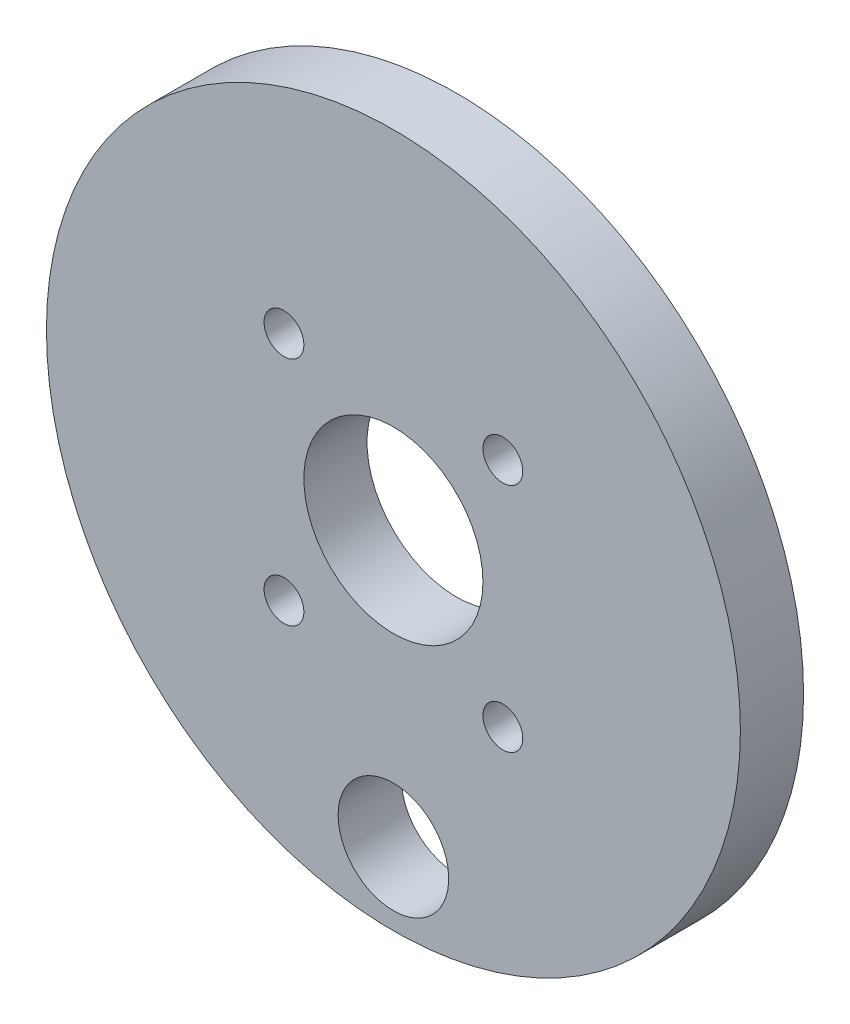
SolidWorks part; units mm, degrees
material "Plain Carbon Steel"
ref_plane "Front Plane" through (0, 0, 0) normal (0, 0, 1) x (1, 0, 0)
ref_plane "Top Plane" through (0, 0, 0) normal (0, 1, 0) x (1, 0, 0)
ref_plane "Right Plane" through (0, 0, 0) normal (1, 0, 0) x (0, 0, -1)
sketch "Sketch1" plane through (0, 0, 0) normal (0, 0, 1) x (1, 0, 0)
  circle A0 centre (0, 0) radius 34.875
  circle A1 centre (0, 0) radius 9
  dimension "D1" = 69.75
  dimension "D2" = 18
extrude "Boss-Extrude1" add sketch "Sketch1" along normal blind 6.35
sketch "Sketch2" plane through (0, 0, 0) normal (0, 0, -1) x (-1, 0, 0)
  circle A0 centre (-11, 11.619) radius 2
  circle A1 centre (11, 11.619) radius 2
  circle A2 centre (11, -11.619) radius 2
  circle A3 centre (-11, -11.619) radius 2
  point P0 (-11, 11.619)
  point P1 (11, 11.619)
  point P3 (11, -11.619)
  point P5 (-11, -11.619)
extrude "Cut-Extrude1" cut sketch "Sketch2" against normal through all
sketch "Sketch3" plane through (0, 0, 0) normal (0, 0, -1) x (-1, 0, 0)
  circle A0 centre (0, -27.5594) radius 5.5563
  dimension "D1" = 11.1125
extrude "Cut-Extrude2" cut sketch "Sketch3" against normal through all
